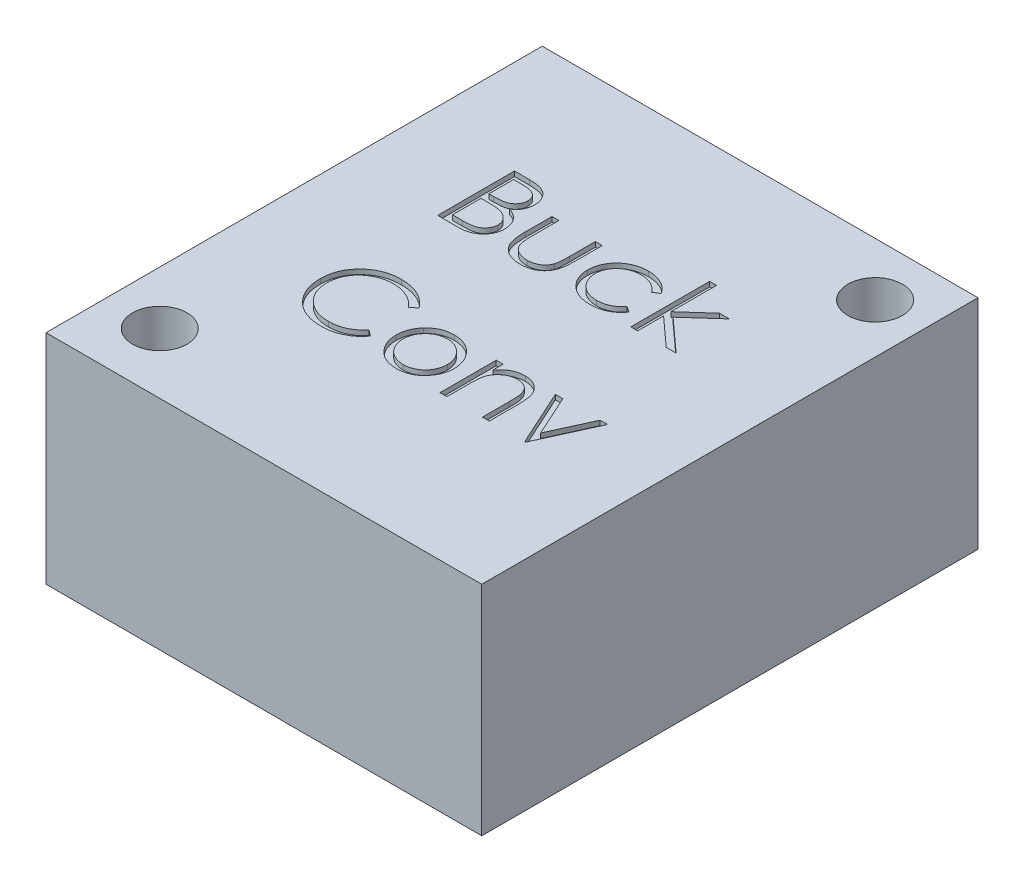
SolidWorks part; units mm, degrees
ref_plane "Front Plane" through (0, 0, 0) normal (0, 0, 1) x (1, 0, 0)
ref_plane "Top Plane" through (0, 0, 0) normal (0, 1, 0) x (1, 0, 0)
ref_plane "Right Plane" through (0, 0, 0) normal (1, 0, 0) x (0, 0, -1)
sketch "Sketch1" plane through (0, 0, 0) normal (0, 1, 0) x (1, 0, 0)
  line L1 (-9, 10.25) -> (9, 10.25)
  line L2 (-9, 10.25) -> (-9, -10.25)
  line L3 (-9, -10.25) -> (9, -10.25)
  line L4 (9, 10.25) -> (9, -10.25)
  line L5 (-9, 10.25) -> (9, -10.25) construction
  line L6 (-9, -10.25) -> (9, 10.25) construction
  circle A0 centre (6.95, 8.05) radius 1.125
  circle A1 centre (-6.8, -7.75) radius 1.125
  point P0 (0, 0)
  dimension "D3" = 2.25
  dimension "D4" = 2.25
  dimension "D1" = 18
  dimension "D2" = 20.5
  dimension "D5" = 13.75
  dimension "D6" = 15.8
  dimension "D7" = 2.2
  dimension "D8" = 2.5
extrude "Boss-Extrude1" add sketch "Sketch1" along normal blind 9
sketch "Sketch3" plane through (0, 9, 0) normal (0, 1, 0) x (1, 0, 0)
  text T0 "Buck\r\nConv"
extrude "Cut-Extrude1" cut sketch "Sketch3" against normal blind 0.2
